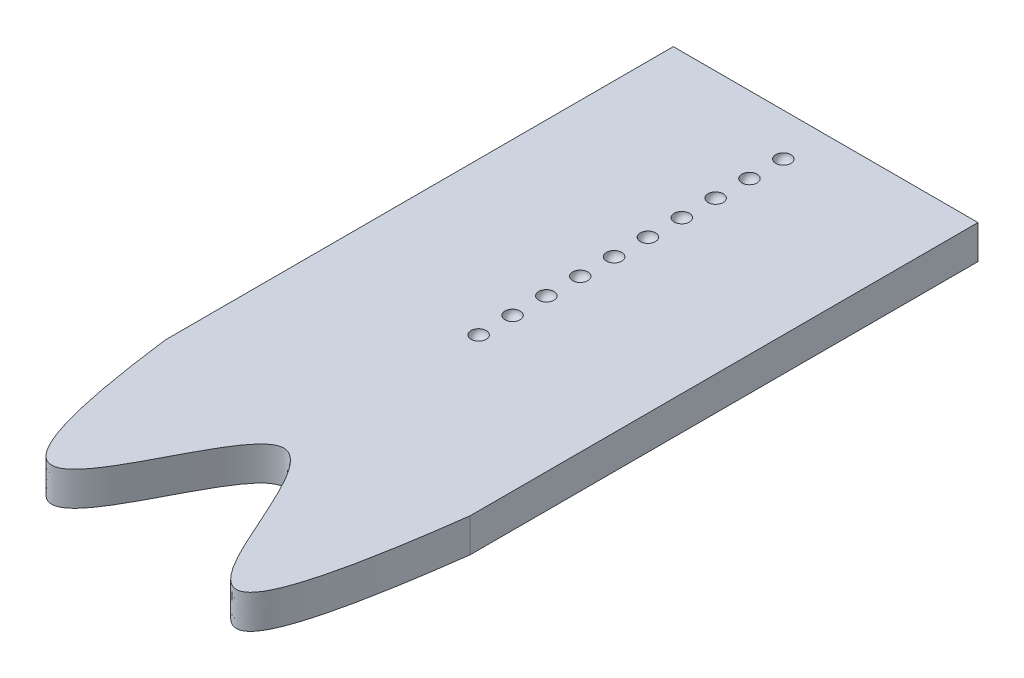
SolidWorks part; units mm, degrees
ref_plane "Front Plane" through (0, 0, 0) normal (0, 0, 1) x (1, 0, 0)
ref_plane "Top Plane" through (0, 0, 0) normal (0, 1, 0) x (1, 0, 0)
ref_plane "Right Plane" through (0, 0, 0) normal (1, 0, 0) x (0, 0, -1)
sketch "Sketch1" plane through (0, 0, 0) normal (0, 1, 0) x (1, 0, 0)
  line L1 (-42.2654, 3.813) -> (3.4546, 3.813)
  line L2 (-42.2654, 3.813) -> (-42.2654, -72.387)
  line L4 (3.4546, 3.813) -> (3.4546, -72.387)
  spline S0 degree 3 poles (-42.2654, -72.387) (-35.6116, -124.8955) (-17.8631, -27.5825) (-4.1879, -130.3974) (3.4546, -72.387) knots 0 0 0 0 0.483362 1 1 1 1
  dimension "D1" = 76.2
  dimension "D2" = 45.72
  dimension "D3" = 12.7
  dimension "D4" = 12.7
  dimension "D5" = 22.86
extrude "Boss-Extrude1" add sketch "Sketch1" along normal blind 5.08
sketch "Sketch2" plane through (0, 5.08, 0) normal (0, 1, 0) x (1, 0, 0)
  line L1 (3.4546, 3.813) -> (-42.2654, 3.813) construction
  line L2 (-20.5484, -2.537) -> (-18.2624, -2.537)
  arc A0 (-18.2624, -2.537) -> (-20.5484, -2.537) centre (-19.4054, -2.537) ccw
  dimension "D2" = 2.286
  dimension "D1" = 6.35
revolve "Cut-Revolve1" cut sketch "Sketch2" angle 360 about L2
pattern_linear "LPattern1" count 10 spacing 5.08 along (0, 0, 1) of "Cut-Revolve1"
